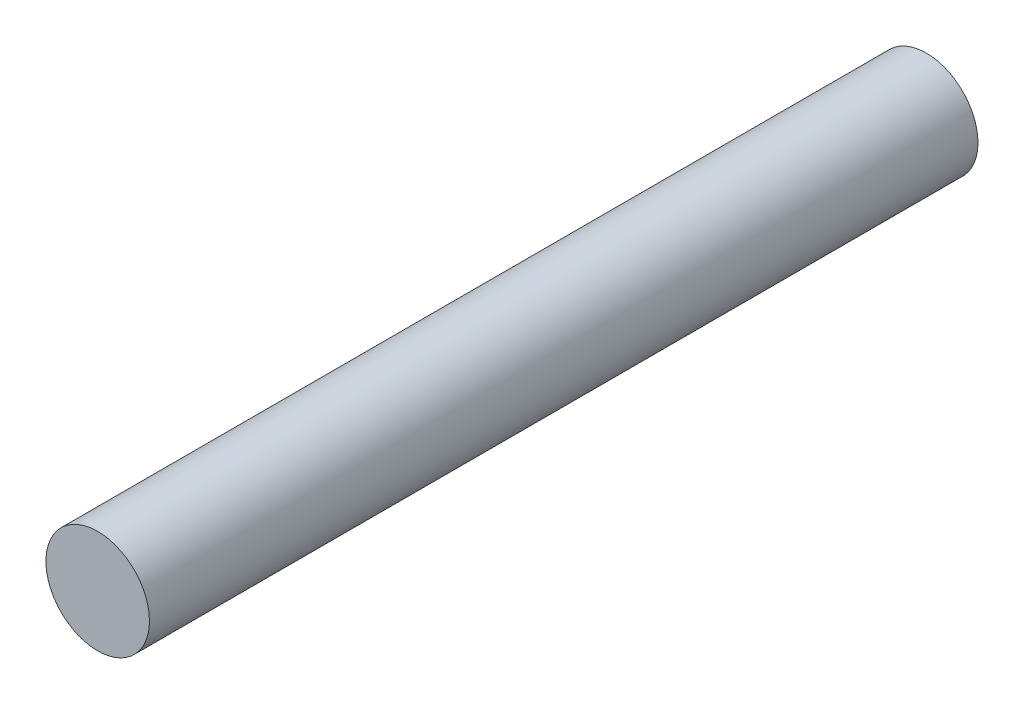
SolidWorks part; units mm, degrees
ref_plane "前视基准面" through (0, 0, 0) normal (0, 0, 1) x (1, 0, 0)
ref_plane "上视基准面" through (0, 0, 0) normal (0, 1, 0) x (1, 0, 0)
ref_plane "右视基准面" through (0, 0, 0) normal (1, 0, 0) x (0, 0, -1)
sketch "草图1" plane through (0, 0, 0) normal (0, 0, 1) x (1, 0, 0)
  circle A0 centre (0, 0) radius 4
  dimension "D1" = 8
extrude "凸台-拉伸1" add sketch "草图1" along normal blind 64
